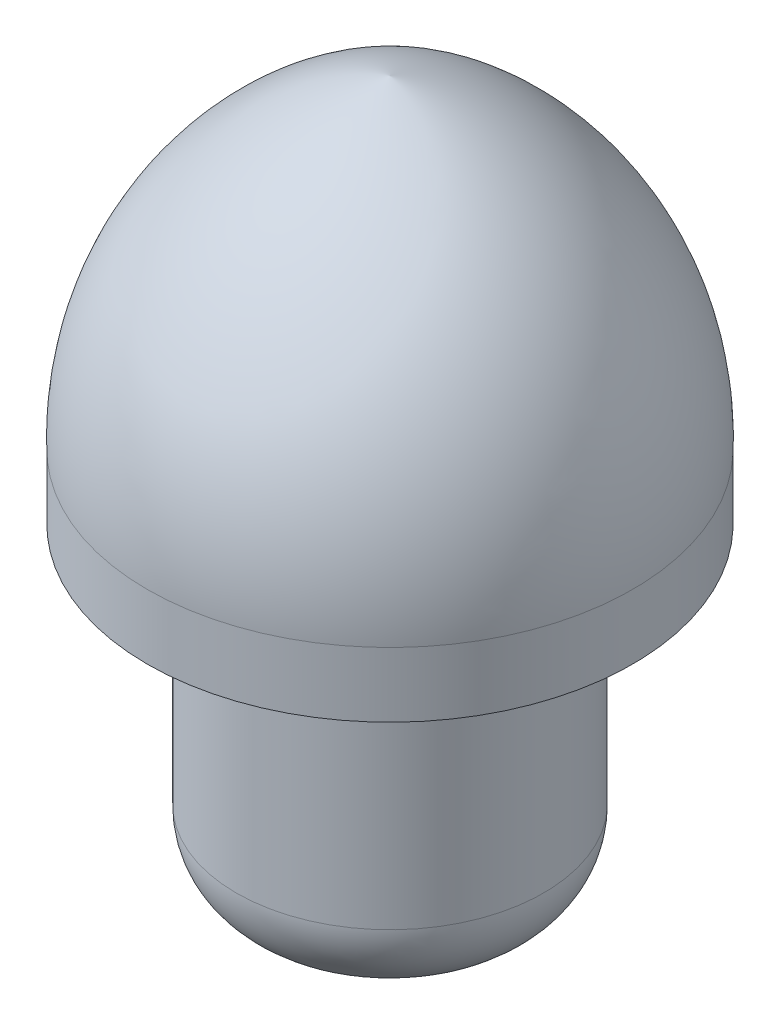
SolidWorks part; units mm, degrees
ref_plane "Plano frontal" through (0, 0, 0) normal (0, 0, 1) x (1, 0, 0)
ref_plane "Plano superior" through (0, 0, 0) normal (0, 1, 0) x (1, 0, 0)
ref_plane "Plano direito" through (0, 0, 0) normal (1, 0, 0) x (0, 0, -1)
sketch "Esboço2" plane through (0, 0, 0) normal (0, 1, 0) x (1, 0, 0)
  circle A0 centre (0, 0) radius 15 construction
  dimension "D1" = 30
sketch "Esboço3" plane through (0, 0, 0) normal (0, 0, 1) x (1, 0, 0)
  line L0 (0, 0) -> (0, 20)
  line L1 (15, 0) -> (-15, 0) construction
  line L2 (-15, 0) -> (-14, 0)
  line L3 (-14, 0) -> (0, 0)
  arc A0 (0, 20) -> (-15, 0) centre (4.99, 0.6325) ccw
  arc A1 (0, 19) -> (-14, 0) centre (5.2642, 0.4632) ccw
  dimension "D2" = 20
  dimension "D1" = 20
  dimension "D3" = 1
  dimension "D4" = 1
revolve "Revolução1" add sketch "Esboço3" angle 360 about L0
sketch "Esboço4" plane through (0, 0, 0) normal (0, 1, 0) x (1, 0, 0)
  circle A0 centre (0, 0) radius 15
extrude "Ressalto-extrusão1" add sketch "Esboço4" against normal blind 4 and the other way blind 1
ref_plane "Plano1" through (0, -4, 0) normal (0, -1, 0) x (-1, 0, 0)
sketch "Esboço5" plane through (0, -4, 0) normal (0, -1, 0) x (-1, 0, 0)
  circle A0 centre (0, 0) radius 9.5
  dimension "D1" = 19
extrude "Ressalto-extrusão2" add sketch "Esboço5" along normal blind 20
fillet "Filete1" radius 5 1 edges at (0, -24, -9.5)
